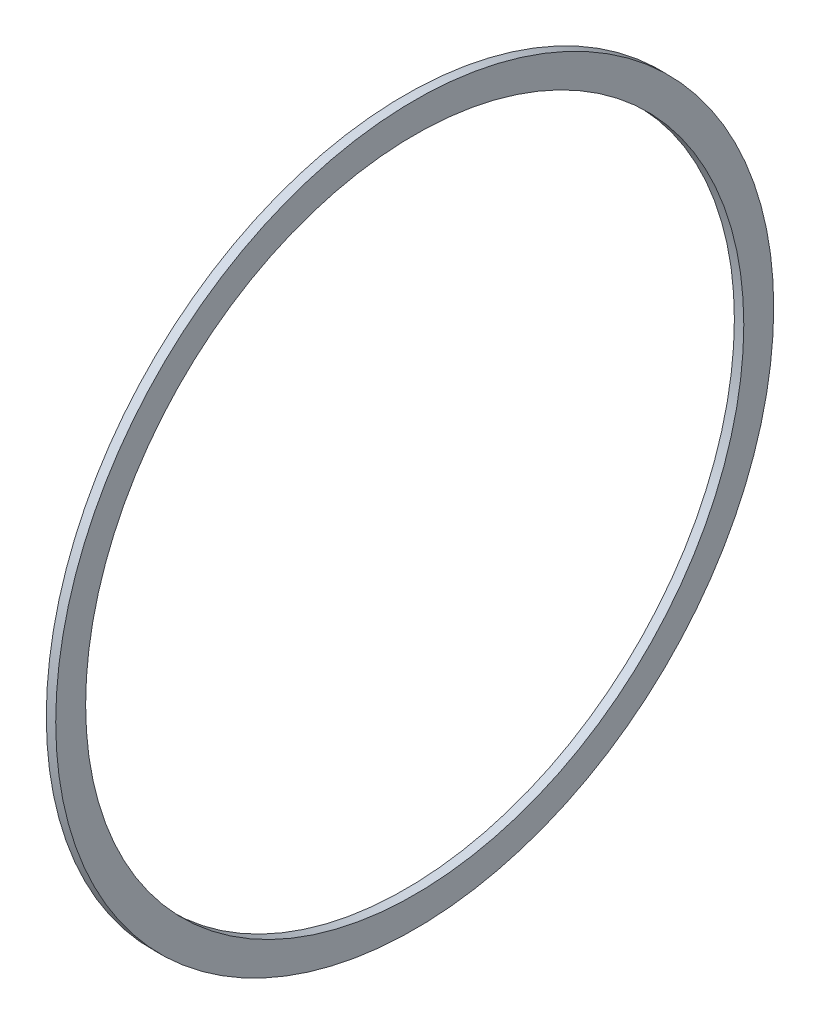
SolidWorks part; units mm, degrees
ref_plane "Front Plane" through (0, 0, 0) normal (0, 0, 1) x (1, 0, 0)
ref_plane "Top Plane" through (0, 0, 0) normal (0, 1, 0) x (1, 0, 0)
ref_plane "Right Plane" through (0, 0, 0) normal (1, 0, 0) x (0, 0, -1)
sketch "Sketch1" plane through (0, 0, 0) normal (1, 0, 0) x (0, 0, -1)
  circle A0 centre (0, 0) radius 69.85
  circle A1 centre (0, 0) radius 76.2
  dimension "D1" = 152.4
  dimension "D2" = 139.7
extrude "Boss-Extrude1" add sketch "Sketch1" along normal mid plane 2
